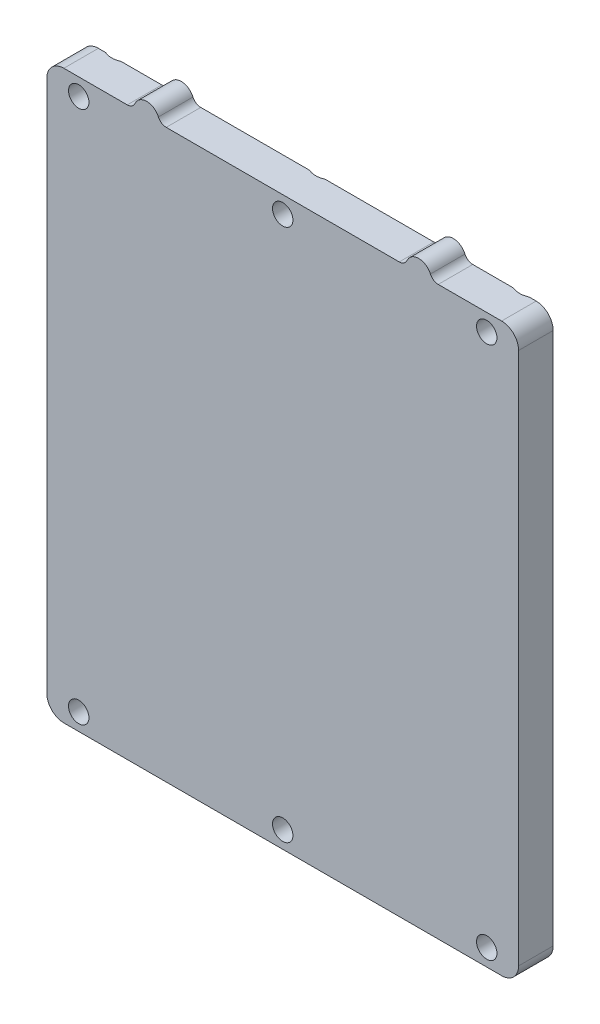
SolidWorks part; units mm, degrees
ref_plane "Front Plane" through (0, 0, 0) normal (0, 0, 1) x (1, 0, 0)
ref_plane "Top Plane" through (0, 0, 0) normal (0, 1, 0) x (1, 0, 0)
ref_plane "Right Plane" through (0, 0, 0) normal (1, 0, 0) x (0, 0, -1)
sketch "Sketch1" plane through (0, 0, 0) normal (0, 0, 1) x (1, 0, 0)
  line L1 (0, 0) -> (55.5, 0)
  line L2 (0, 0) -> (0, 66.7)
  line L3 (0, 66.7) -> (55.5, 66.7)
  line L4 (55.5, 0) -> (55.5, 66.7)
  dimension "D1" = 55.5
  dimension "D2" = 66.7
extrude "Boss-Extrude1" add sketch "Sketch1" along normal blind 4.064
hole_wizard "CSK for M2 Flat Head Machine Screw3" positions "Sketch6" profile "Sketch5" countersink size "M2" standard "ANSI Metric" end condition through all
sketch "Sketch6" plane through (2.7835, 10.3926, 0) normal (0, 0, 1) x (1, 0, 0)
  line L0 (-2.7835, 54.3074) -> (0.9665, 54.3074) construction
  line L1 (-2.7835, 56.3074) -> (-2.7835, -10.3926) construction
  line L6 (48.9665, 54.3074) -> (52.7165, 54.3074) construction
  line L7 (52.7165, -10.3926) -> (52.7165, 56.3074) construction
  line L9 (52.7165, 56.3074) -> (-2.7835, 56.3074) construction
  line L11 (24.9665, 56.3074) -> (24.9665, -10.3926) construction
  line L12 (-2.7835, -10.3926) -> (52.7165, -10.3926) construction
  line L14 (0.9665, -8.3926) -> (0.9665, 54.3074) construction
  line L16 (0.9665, 22.9574) -> (-2.7835, 22.9574) construction
  line L17 (-2.7835, 56.3074) -> (-2.7835, -10.3926) construction
  point P0 (0.9665, 54.3074)
  point P4 (24.9665, 54.3074)
  point P8 (48.9665, 54.3074)
  point P33 (0.9665, -8.3926)
  point P35 (24.9665, -8.3926)
  point P41 (48.9665, -8.3926)
  dimension "D1" = 24
  dimension "D2" = 62.7
sketch "Sketch5" plane through (3.75, 64.7, 0) normal (1, 0, 0) x (0, 1, 0)
  line L0 (0, 0) -> (0, 4.064)
  line L1 (0, 4.064) -> (1.2, 4.064)
  line L2 (1.2, 4.064) -> (1.2, 1)
  line L3 (1.2, 1) -> (2.2, 0)
  line L5 (2.2, 0) -> (0, 0)
  line L6 (-1.2, 1) -> (-2.2, 0) construction
  line L11 (0, -6.35) -> (0, 107.95) construction
  dimension "Thru Hole Dia." = 2.4
  dimension "Thru Hole Depth" = 4.064
  dimension "Near C'Sink Dia." = 4.4
  dimension "Near C'Sink Angle" = 90
fillet "Fillet1" radius 2 4 edges at (55.5, 0, 2.032) (0, 0, 2.032) (55.5, 66.7, 2.032) (0, 66.7, 2.032)
sketch "Sketch7" plane through (0, 0, 4.064) normal (0, 0, 1) x (1, 0, 0)
  line L0 (53.5, 66.7) -> (2, 66.7) construction
  line L2 (11.75, 68.2) -> (43.75, 68.2) construction
  line L3 (27.75, 68.2) -> (27.75, 66.7) construction
  line L4 (10.25, 66.7) -> (13.25, 66.7)
  line L5 (42.25, 66.7) -> (45.25, 66.7)
  arc A0 (45.25, 66.7) -> (42.25, 66.7) centre (43.75, 66.7) ccw
  arc A1 (13.25, 66.7) -> (10.25, 66.7) centre (11.75, 66.7) ccw
  dimension "D2" = 1.5
  dimension "D1" = 32
extrude "Boss-Extrude3" add sketch "Sketch7" against normal through all
fillet "Fillet2" radius 1 4 edges at (13.25, 66.7, 2.032) (10.25, 66.7, 2.032) (45.25, 66.7, 2.032) (42.25, 66.7, 2.032)
hole_wizard "M2 Clearance Hole1" positions "Sketch9" profile "Sketch8" hole size "M2" standard "ANSI Metric"
sketch "Sketch9" plane through (0, 0, 4) normal (0, 0, 1) x (1, 0, 0)
  line L0 (7.75, 68.2) -> (7.75, 2.5) construction
  line L2 (47.75, 68.2) -> (47.75, 2.5) construction
  line L4 (7.75, 2.5) -> (47.75, 2.5) construction
  line L6 (2, 0) -> (53.5, 0) construction
  arc A0 (9.1248, 67.3) -> (6.3752, 67.3) centre (7.75, 66.7) ccw construction
  arc A1 (49.1248, 67.3) -> (46.3752, 67.3) centre (47.75, 66.7) ccw construction
  point P0 (7.75, 2.5)
  point P2 (47.75, 2.5)
  dimension "D1" = 2.5
sketch "Sketch8" plane through (7.75, 2.5, 4) normal (1, 0, 0) x (0, -1, 0)
  line L0 (0, 0) -> (0, 4)
  line L1 (0, 4) -> (1.2, 4)
  line L2 (1.2, 4) -> (1.2, 0)
  line L5 (1.2, 0) -> (0, 0)
  line L11 (0, -6.35) -> (0, 107.95) construction
  dimension "Thru Hole Dia." = 2.4
  dimension "Thru Hole Depth" = 4
